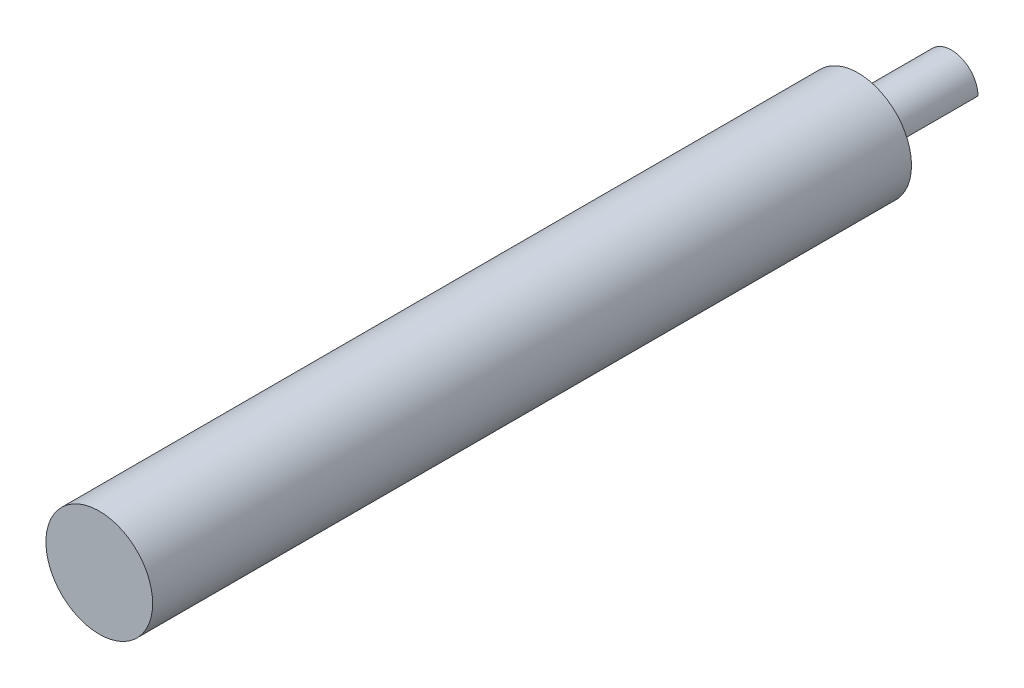
SolidWorks part; units mm, degrees
material "AISI 1020"
ref_plane "Front Plane" through (0, 0, 0) normal (0, 0, 1) x (1, 0, 0)
ref_plane "Top Plane" through (0, 0, 0) normal (0, 1, 0) x (1, 0, 0)
ref_plane "Right Plane" through (0, 0, 0) normal (1, 0, 0) x (0, 0, -1)
sketch "Sketch1" plane through (0, 0, 0) normal (0, 0, 1) x (1, 0, 0)
  circle A0 centre (0, 0) radius 3.1623
  dimension "D1" = 6.3246
extrude "Boss-Extrude1" add sketch "Sketch1" along normal blind 11.0998
sketch "Sketch2" plane through (0, 0, 0) normal (0, 0, -1) x (-1, 0, 0)
  line L0 (0.0012, -3.1623) -> (-3.1623, 0.0012)
  circle A0 centre (0, 0) radius 3.1623 construction
  dimension "D1" = 2.2352
extrude "Cut-Extrude1" cut sketch "Sketch2" against normal through all and the other way through all
sketch "Sketch3" plane through (0, 0, 11.0998) normal (0, 0, 1) x (1, 0, 0)
  circle A0 centre (0, 0) radius 6.35
  dimension "D1" = 12.7
extrude "Boss-Extrude2" add sketch "Sketch3" along normal blind 90.297
sketch "Sketch5" plane through (0, 0, 101.3968) normal (0, 0, 1) x (1, 0, 0)
  circle A0 centre (0, 0) radius 6.35
fillet "Fillet1" radius 1.27 2 edges at (-2.2361, 2.2361, 11.0998) (1.5805, -1.5805, 11.0998)
